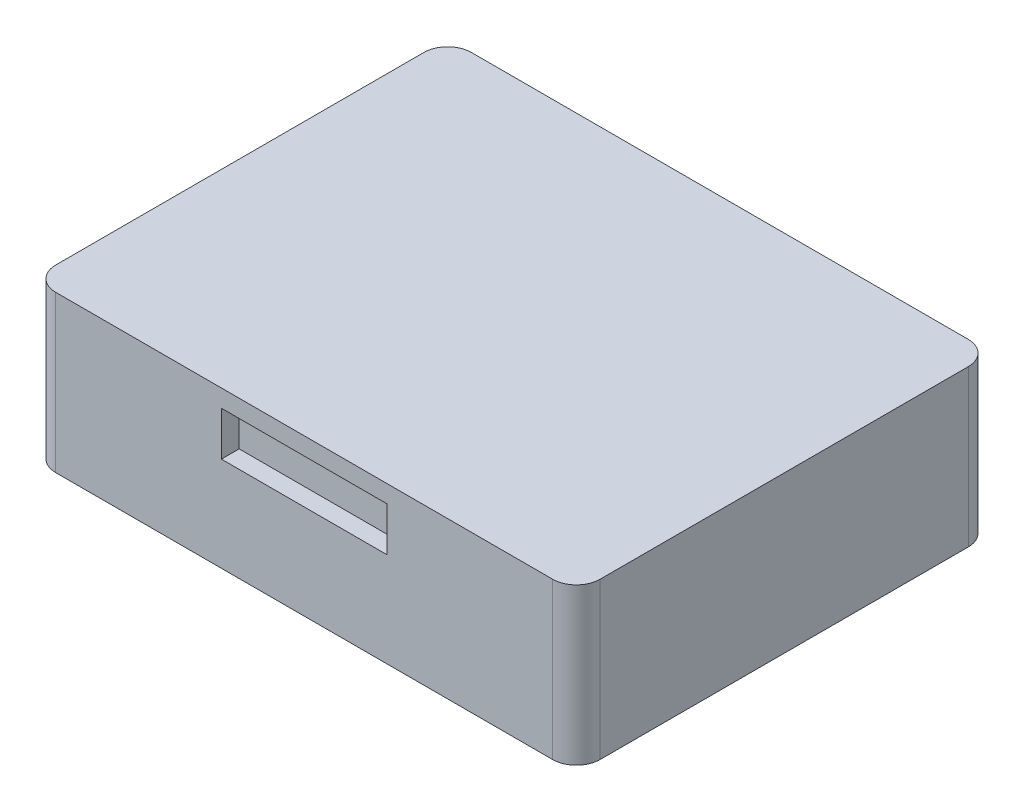
SolidWorks part; units mm, degrees
ref_plane "Front Plane" through (0, 0, 0) normal (0, 0, 1) x (1, 0, 0)
ref_plane "Top Plane" through (0, 0, 0) normal (0, 1, 0) x (1, 0, 0)
ref_plane "Right Plane" through (0, 0, 0) normal (1, 0, 0) x (0, 0, -1)
sketch "Sketch1" plane through (0, 0, 0) normal (0, 1, 0) x (1, 0, 0)
  line L1 (23, -17.56) -> (-23, -17.56)
  line L2 (23, -17.56) -> (23, 17.56)
  line L3 (23, 17.56) -> (-23, 17.56)
  line L4 (-23, -17.56) -> (-23, 17.56)
  line L5 (23, -17.56) -> (-23, 17.56) construction
  line L6 (23, 17.56) -> (-23, -17.56) construction
  point P0 (0, 0)
  dimension "D1" = 46
  dimension "D2" = 35.12
extrude "Boss-Extrude1" add sketch "Sketch1" along normal blind 13.2
sketch "Sketch2" plane through (0, 0, -17.56) normal (0, 0, -1) x (-1, 0, 0)
  line L1 (-4.3202, 6.259) -> (-17.5702, 6.259)
  line L2 (-4.3202, 6.259) -> (-4.3202, 11.589)
  line L3 (-4.3202, 11.589) -> (-17.5702, 11.589)
  line L4 (-17.5702, 6.259) -> (-17.5702, 11.589)
  line L5 (-4.3202, 6.259) -> (-17.5702, 11.589) construction
  line L6 (-4.3202, 11.589) -> (-17.5702, 6.259) construction
  point P0 (-10.9452, 8.924)
  dimension "D1" = 13.25
  dimension "D2" = 5.33
extrude "Cut-Extrude1" cut sketch "Sketch2" against normal blind 1.5
sketch "Sketch5" plane through (0, 0, -17.56) normal (0, 0, -1) x (-1, 0, 0)
  line L1 (17.0711, 6.2137) -> (3.8211, 6.2137)
  line L2 (17.0711, 6.2137) -> (17.0711, 11.5437)
  line L3 (17.0711, 11.5437) -> (3.8211, 11.5437)
  line L4 (3.8211, 6.2137) -> (3.8211, 11.5437)
  line L5 (17.0711, 6.2137) -> (3.8211, 11.5437) construction
  line L6 (17.0711, 11.5437) -> (3.8211, 6.2137) construction
  point P0 (10.4461, 8.8787)
  dimension "D1" = 13.25
  dimension "D2" = 5.33
extrude "Cut-Extrude2" cut sketch "Sketch5" against normal blind 1.5 contours L1 L4 L3 L2
sketch "Sketch6" plane through (0, 0, 17.56) normal (0, 0, 1) x (1, 0, 0)
  line L1 (7, 7.9919) -> (-7, 7.9919)
  line L2 (7, 7.9919) -> (7, 11.7179)
  line L3 (7, 11.7179) -> (-7, 11.7179)
  line L4 (-7, 7.9919) -> (-7, 11.7179)
  line L5 (7, 7.9919) -> (-7, 11.7179) construction
  line L6 (7, 11.7179) -> (-7, 7.9919) construction
  point P0 (0, 9.8549)
  dimension "D1" = 14
extrude "Cut-Extrude3" cut sketch "Sketch6" against normal blind 1.5
fillet "Fillet1" radius 2 4 edges at (-23, 6.6, -17.56) (23, 6.6, -17.56) (-23, 6.6, 17.56) (23, 6.6, 17.56)
